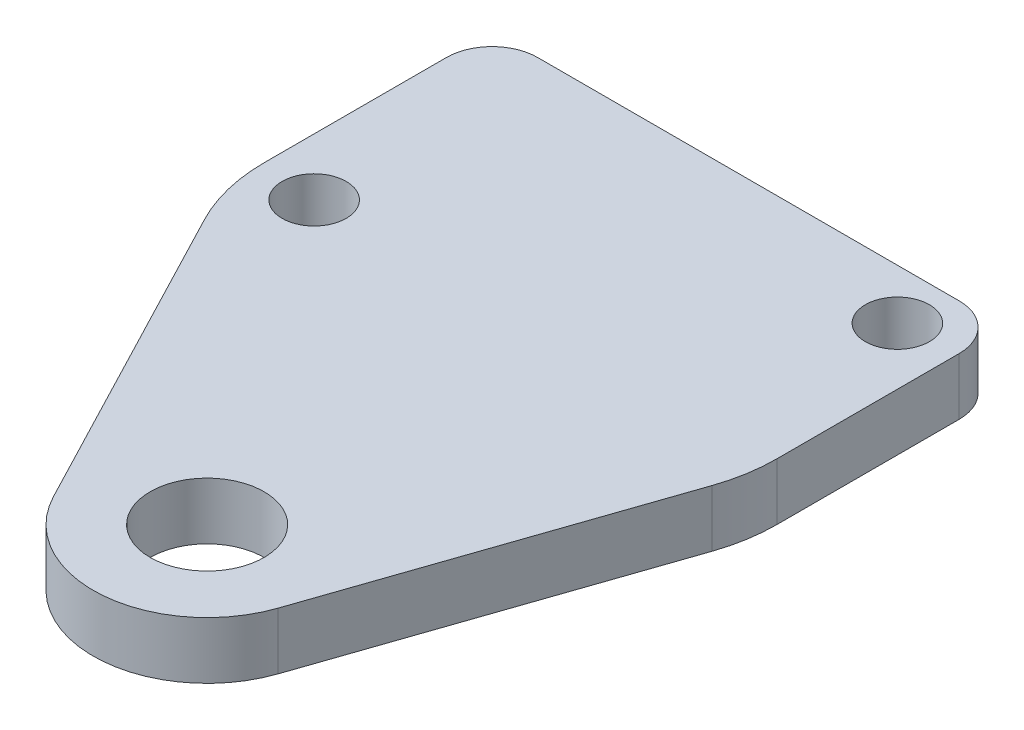
SolidWorks part; units mm, degrees
material "6061-T6 (SS)"
ref_plane "Front Plane" through (0, 0, 0) normal (0, 0, 1) x (1, 0, 0)
ref_plane "Top Plane" through (0, 0, 0) normal (0, 1, 0) x (1, 0, 0)
ref_plane "Right Plane" through (0, 0, 0) normal (1, 0, 0) x (0, 0, -1)
sketch "Sketch1" plane through (0, 0, 0) normal (0, 1, 0) x (1, 0, 0)
  line L0 (-14.7963, 14.6471) -> (-5.6309, -2.9353)
  line L1 (-15.875, 31.75) -> (12.7, 31.75)
  line L2 (-15.875, 31.75) -> (-15.875, 19.05)
  line L3 (-15.875, 19.05) -> (12.7, 19.05) construction
  line L4 (12.7, 31.75) -> (12.7, 19.05)
  line L5 (12.1851, 15.9608) -> (6.0068, -2.0595)
  circle A0 centre (0, 0) radius 3.175
  circle A1 centre (0, 0) radius 6.35 construction
  arc A4 (-15.875, 19.05) -> (-14.7963, 14.6471) centre (-6.35, 19.05) ccw
  arc A5 (12.7, 19.05) -> (12.1851, 15.9608) centre (3.175, 19.05) cw
  arc A6 (-5.6309, -2.9353) -> (6.0068, -2.0595) centre (0, 0) ccw
  point P18 (-15.6088, 24.769)
  point P19 (-9.2111, 18.4465)
  point P20 (-12.3564, 2.0203)
  dimension "D1" = 6.35
  dimension "D2" = 12.7
  dimension "D7" = 9.525
  dimension "D3" = 12.7
  dimension "D4" = 28.575
  dimension "D5" = 31.75
  dimension "D6" = 15.875
extrude "Boss-Extrude1" add sketch "Sketch1" along normal blind 3.175
sketch "Sketch2" plane through (0, 3.175, 0) normal (0, 1, 0) x (1, 0, 0)
  line L0 (-12.4625, 18.65) -> (-12.9125, 18.65) construction
  circle A0 centre (9.5125, 28.95) radius 1.55 construction
  circle A1 centre (9.5125, 28.95) radius 1.55 construction
  circle A2 centre (-12.6875, 18.65) radius 1.7859
  arc A3 (-12.9125, 20.2) -> (-12.9125, 17.1) centre (-12.9125, 18.65) ccw construction
  arc A4 (-12.4625, 17.1) -> (-12.4625, 20.2) centre (-12.4625, 18.65) ccw construction
  arc A5 (-12.9125, 20.2) -> (-12.9125, 17.1) centre (-12.9125, 18.65) ccw construction
  arc A6 (-12.4625, 17.1) -> (-12.4625, 20.2) centre (-12.4625, 18.65) ccw construction
  circle A7 centre (9.5125, 28.95) radius 1.7859
  dimension "D1" = 3.5719
extrude "Cut-Extrude1" cut sketch "Sketch2" against normal through all
fillet "Fillet1" radius 2.54 2 edges at (12.7, 1.5875, -31.75) (-15.875, 1.5875, -31.75)
